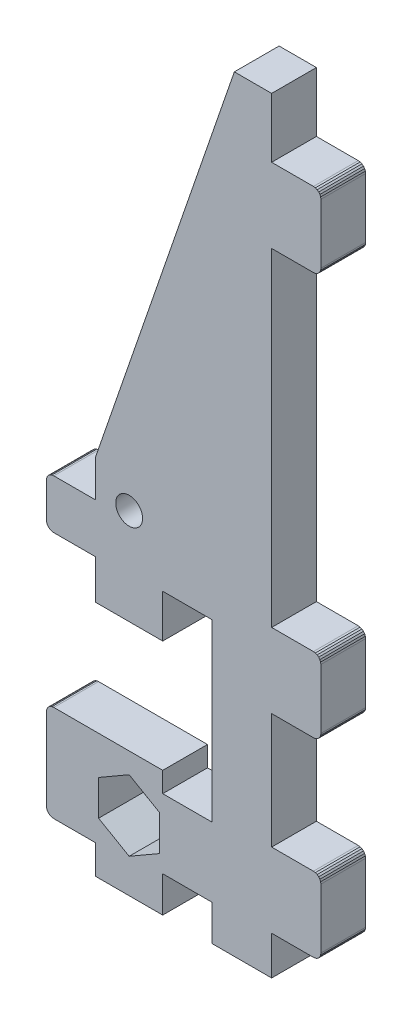
SolidWorks part; units mm, degrees
ref_plane "Plano frontal" through (0, 0, 0) normal (0, 0, 1) x (1, 0, 0)
ref_plane "Plano superior" through (0, 0, 0) normal (0, 1, 0) x (1, 0, 0)
ref_plane "Plano direito" through (0, 0, 0) normal (1, 0, 0) x (0, 0, -1)
sketch "Model" plane through (0, 0, 0) normal (0, 0, 1) x (1, 0, 0)
  line L0 (64.5442, 102.0853) -> (58.9442, 102.0853)
  line L1 (65.5102, 101.3442) -> (65.5442, 101.0853)
  line L2 (35.3442, 39.2028) -> (44.3442, 39.2028)
  line L3 (65.0442, 38.2193) -> (65.2513, 38.3782)
  line L4 (35.3442, 7.3871) -> (44.3405, 7.3871)
  line L5 (58.9442, 110.0853) -> (53.9442, 110.0853)
  line L6 (35.3442, 11.2853) -> (29.7442, 11.2853)
  line L7 (44.3442, 12.1905) -> (50.9442, 12.1853)
  line L8 (50.9442, 12.1853) -> (50.9405, 7.3871)
  line L9 (35.3442, 51.0853) -> (35.3442, 56.0853)
  line L10 (58.9442, 38.0853) -> (58.9442, 22.5853)
  line L11 (64.5442, 92.0853) -> (58.9442, 92.0853)
  line L12 (58.9442, 92.0853) -> (58.9442, 48.0853)
  line L13 (44.3405, 7.3871) -> (44.3442, 12.1905)
  line L14 (28.8782, 23.6976) -> (29.0371, 23.9047)
  line L15 (35.3442, 44.4853) -> (35.3442, 39.2028)
  line L16 (44.3442, 21.4853) -> (50.9442, 21.4853)
  line L17 (58.9442, 110.0853) -> (58.9442, 102.0853)
  line L18 (29.7442, 44.4853) -> (35.3442, 44.4853)
  line L19 (29.7442, 44.4853) -> (29.4854, 44.5194)
  line L20 (29.4854, 44.5194) -> (29.2442, 44.6193)
  line L21 (29.2442, 44.6193) -> (29.0371, 44.7782)
  line L22 (64.5442, 22.5853) -> (64.8031, 22.5513)
  line L23 (29.2442, 11.4193) -> (29.0371, 11.5782)
  line L24 (29.0371, 11.5782) -> (28.8782, 11.7853)
  line L25 (28.8782, 11.7853) -> (28.7783, 12.0265)
  line L26 (65.5442, 93.0853) -> (65.5442, 101.0853)
  line L27 (28.7783, 12.0265) -> (28.7442, 12.2853)
  line L28 (65.0442, 47.9514) -> (65.2513, 47.7924)
  line L29 (65.2513, 47.7924) -> (65.4103, 47.5853)
  line L30 (65.5102, 13.3265) -> (65.4103, 13.0853)
  line L31 (65.4103, 13.0853) -> (65.2513, 12.8782)
  line L32 (65.2513, 12.8782) -> (65.0442, 12.7193)
  line L33 (65.0442, 12.7193) -> (64.8031, 12.6194)
  line L34 (64.8031, 12.6194) -> (64.5442, 12.5853)
  line L35 (64.5442, 102.0853) -> (64.8031, 102.0513)
  line L36 (29.0371, 23.9047) -> (29.2442, 24.0636)
  line L37 (29.2442, 24.0636) -> (29.4854, 24.1635)
  line L38 (29.4854, 24.1635) -> (29.7442, 24.1976)
  line L39 (64.8031, 38.1194) -> (65.0442, 38.2193)
  line L40 (64.5442, 38.0853) -> (64.8031, 38.1194)
  line L41 (64.5442, 38.0853) -> (58.9442, 38.0853)
  line L42 (65.0442, 22.4514) -> (65.2513, 22.2924)
  line L43 (65.2513, 22.2924) -> (65.4103, 22.0853)
  line L44 (29.0371, 50.7924) -> (28.8782, 50.5853)
  line L45 (28.8782, 50.5853) -> (28.7783, 50.3442)
  line L46 (28.7442, 50.0853) -> (28.7442, 45.4853)
  line L47 (28.7783, 50.3442) -> (28.7442, 50.0853)
  line L48 (65.2513, 38.3782) -> (65.4103, 38.5853)
  line L49 (65.4103, 38.5853) -> (65.5102, 38.8265)
  line L50 (65.5442, 39.0853) -> (65.5442, 47.0853)
  line L51 (65.5102, 38.8265) -> (65.5442, 39.0853)
  line L52 (50.9442, 44.9853) -> (44.3442, 44.9853)
  line L53 (53.9442, 110.0853) -> (35.3442, 56.0853)
  line L54 (64.5442, 48.0853) -> (58.9442, 48.0853)
  line L55 (64.5442, 48.0853) -> (64.8031, 48.0513)
  line L56 (64.8031, 48.0513) -> (65.0442, 47.9514)
  line L57 (28.7442, 23.1976) -> (28.7783, 23.4564)
  line L58 (28.7783, 23.4564) -> (28.8782, 23.6976)
  line L59 (29.7442, 24.1976) -> (44.3442, 24.1976)
  line L60 (65.5442, 93.0853) -> (65.5102, 92.8265)
  line L61 (65.5102, 92.8265) -> (65.4103, 92.5853)
  line L62 (65.4103, 92.5853) -> (65.2513, 92.3782)
  line L63 (65.2513, 92.3782) -> (65.0442, 92.2193)
  line L64 (65.0442, 92.2193) -> (64.8031, 92.1194)
  line L65 (64.8031, 92.1194) -> (64.5442, 92.0853)
  line L66 (50.9405, 7.3871) -> (58.9442, 7.3871)
  line L67 (58.9442, 12.5853) -> (58.9442, 7.3871)
  line L68 (64.5442, 12.5853) -> (58.9442, 12.5853)
  line L69 (65.5442, 13.5853) -> (65.5102, 13.3265)
  line L70 (65.5442, 13.5853) -> (65.5442, 21.5853)
  line L71 (65.5102, 21.8442) -> (65.5442, 21.5853)
  line L72 (65.4103, 22.0853) -> (65.5102, 21.8442)
  line L73 (64.8031, 22.5513) -> (65.0442, 22.4514)
  line L74 (58.9442, 22.5853) -> (64.5442, 22.5853)
  line L75 (65.5102, 47.3442) -> (65.5442, 47.0853)
  line L76 (65.4103, 47.5853) -> (65.5102, 47.3442)
  line L77 (65.4103, 101.5853) -> (65.5102, 101.3442)
  line L78 (65.2513, 101.7924) -> (65.4103, 101.5853)
  line L79 (65.0442, 101.9514) -> (65.2513, 101.7924)
  line L80 (64.8031, 102.0513) -> (65.0442, 101.9514)
  line L81 (29.7442, 51.0853) -> (35.3442, 51.0853)
  line L82 (29.7442, 51.0853) -> (29.4854, 51.0513)
  line L83 (29.4854, 51.0513) -> (29.2442, 50.9514)
  line L84 (29.2442, 50.9514) -> (29.0371, 50.7924)
  line L85 (28.7783, 45.2265) -> (28.7442, 45.4853)
  line L86 (28.8782, 44.9853) -> (28.7783, 45.2265)
  line L87 (29.0371, 44.7782) -> (28.8782, 44.9853)
  line L88 (44.3442, 44.9853) -> (44.3442, 39.2028)
  line L89 (50.9442, 21.4853) -> (50.9442, 44.9853)
  line L90 (44.3442, 24.1976) -> (44.3442, 21.4853)
  line L91 (28.7442, 23.1976) -> (28.7442, 12.2853)
  line L92 (29.4854, 11.3194) -> (29.2442, 11.4193)
  line L93 (29.7442, 11.2853) -> (29.4854, 11.3194)
  line L94 (35.3442, 11.2853) -> (35.3442, 7.3871)
  line L95 (43.9442, 19.0699) -> (39.8442, 21.4371)
  line L96 (39.8442, 21.4371) -> (35.7442, 19.0699)
  line L97 (35.7442, 19.0699) -> (35.7442, 14.3357)
  line L98 (35.7442, 14.3357) -> (39.8442, 11.9685)
  line L99 (39.8442, 11.9685) -> (43.9442, 14.3357)
  line L100 (43.9442, 14.3357) -> (43.9442, 19.0699)
  circle A0 centre (39.8442, 52.0853) radius 1.8
extrude "Ressalto-extrusão1" add sketch "Model" along normal blind 6
ref_plane "Plano1" through (0, 0, 3) normal (0, 0, 1) x (1, 0, 0)
ref_plane "Plano3" through (0, 57.3353, 0) normal (0, -1, 0) x (-1, 0, 0)
ref_plane "Plano4" through (0, 31.1853, 0) normal (0, -1, 0) x (-1, 0, 0)
